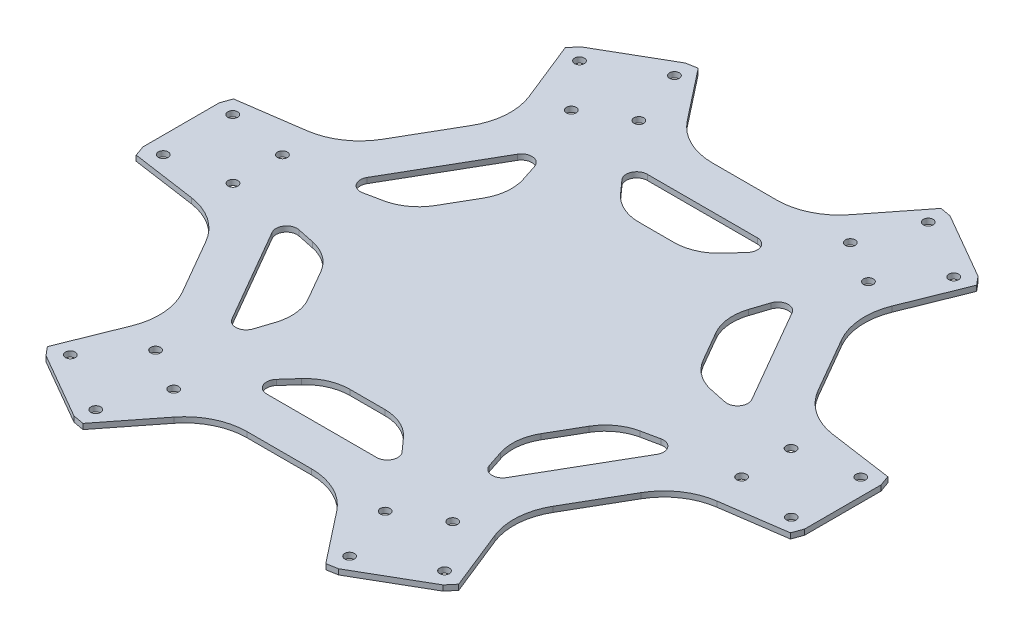
SolidWorks part; units mm, degrees
ref_plane "Front Plane" through (0, 0, 0) normal (0, 0, 1) x (1, 0, 0)
ref_plane "Top Plane" through (0, 0, 0) normal (0, 1, 0) x (1, 0, 0)
ref_plane "Right Plane" through (0, 0, 0) normal (1, 0, 0) x (0, 0, -1)
sketch "Model" plane through (0, 0, 0) normal (0, 1, 0) x (1, 0, 0)
  line L0 (-40.4555, -102.4939) -> (-44.0829, -101.8523)
  line L1 (-27.0946, -85.4828) -> (-40.4555, -102.4939)
  line L2 (-10.7284, -77.5264) -> (10.7284, -77.5264)
  line L3 (27.0946, -85.4828) -> (40.4555, -102.4939)
  line L4 (44.0829, -101.8523) -> (66.1652, -89.1031)
  line L5 (40.4555, -102.4939) -> (44.0829, -101.8523)
  line L6 (68.5346, -86.2824) -> (66.1652, -89.1031)
  line L7 (60.483, -66.206) -> (68.5346, -86.2824)
  line L8 (61.7757, -48.0543) -> (72.5041, -29.4721)
  line L9 (87.5776, -19.2768) -> (108.99, -16.2115)
  line L10 (110.2482, -12.7492) -> (110.2482, 12.7492)
  line L11 (108.99, -16.2115) -> (110.2482, -12.7492)
  line L12 (108.99, 16.2115) -> (110.2482, 12.7492)
  line L13 (87.5776, 19.2768) -> (108.99, 16.2115)
  line L14 (72.5041, 29.4721) -> (61.7757, 48.0543)
  line L15 (60.483, 66.206) -> (68.5346, 86.2824)
  line L16 (66.1652, 89.1031) -> (44.0829, 101.8523)
  line L17 (68.5346, 86.2824) -> (66.1652, 89.1031)
  line L18 (40.4555, 102.4939) -> (44.0829, 101.8523)
  line L19 (27.0946, 85.4828) -> (40.4555, 102.4939)
  line L20 (10.7284, 77.5264) -> (-10.7284, 77.5264)
  line L21 (-27.0946, 85.4828) -> (-40.4555, 102.4939)
  line L22 (-44.0829, 101.8523) -> (-66.1652, 89.1031)
  line L23 (-40.4555, 102.4939) -> (-44.0829, 101.8523)
  line L24 (-68.5346, 86.2824) -> (-66.1652, 89.1031)
  line L25 (-60.483, 66.206) -> (-68.5346, 86.2824)
  line L26 (-61.7757, 48.0543) -> (-72.5041, 29.4721)
  line L27 (-87.5776, 19.2768) -> (-108.99, 16.2115)
  line L28 (-110.2482, 12.7492) -> (-110.2482, -12.7492)
  line L29 (-108.99, 16.2115) -> (-110.2482, 12.7492)
  line L30 (-108.99, -16.2115) -> (-110.2482, -12.7492)
  line L31 (-87.5776, -19.2768) -> (-108.99, -16.2115)
  line L32 (-72.5041, -29.4721) -> (-61.7757, -48.0543)
  line L33 (-60.483, -66.206) -> (-68.5346, -86.2824)
  line L34 (-66.1652, -89.1031) -> (-44.0829, -101.8523)
  line L35 (-68.5346, -86.2824) -> (-66.1652, -89.1031)
  line L36 (18.3454, -63.4119) -> (-18.3454, -63.4119)
  line L37 (17.0052, -53.1705) -> (20.9523, -57.5765)
  line L38 (-5.8327, -48.1793) -> (5.8327, -48.1793)
  line L39 (-20.9523, -57.5765) -> (-17.0052, -53.1705)
  line L40 (64.089, -15.8183) -> (45.7436, -47.5935)
  line L41 (54.5496, -11.8583) -> (60.3389, -10.643)
  line L42 (38.8081, -29.141) -> (44.6409, -19.0383)
  line L43 (39.3866, -46.9335) -> (37.5444, -41.3122)
  line L44 (45.7436, 47.5935) -> (64.089, 15.8183)
  line L45 (37.5444, 41.3122) -> (39.3866, 46.9335)
  line L46 (44.6409, 19.0383) -> (38.8081, 29.141)
  line L47 (60.3389, 10.643) -> (54.5496, 11.8583)
  line L48 (-18.3454, 63.4119) -> (18.3454, 63.4119)
  line L49 (-17.0052, 53.1705) -> (-20.9523, 57.5765)
  line L50 (5.8327, 48.1793) -> (-5.8327, 48.1793)
  line L51 (20.9523, 57.5765) -> (17.0052, 53.1705)
  line L52 (-64.089, 15.8183) -> (-45.7436, 47.5935)
  line L53 (-54.5496, 11.8583) -> (-60.3389, 10.643)
  line L54 (-38.8081, 29.141) -> (-44.6409, 19.0383)
  line L55 (-39.3866, 46.9335) -> (-37.5444, 41.3122)
  line L56 (-45.7436, -47.5935) -> (-64.089, -15.8183)
  line L57 (-37.5444, -41.3122) -> (-39.3866, -46.9335)
  line L58 (-44.6409, -19.0383) -> (-38.8081, -29.141)
  line L59 (-60.3389, -10.643) -> (-54.5496, -11.8583)
  circle A0 centre (49.4999, -69.2617) radius 1.625
  circle A1 centre (35.2325, -77.499) radius 1.625
  circle A2 centre (42.2879, -96.4) radius 1.625
  circle A3 centre (62.3409, -84.8224) radius 1.625
  circle A4 centre (84.7323, 8.2373) radius 1.625
  circle A5 centre (84.7323, -8.2373) radius 1.625
  circle A6 centre (104.6288, -11.5776) radius 1.625
  circle A7 centre (104.6288, 11.5776) radius 1.625
  circle A8 centre (35.2325, 77.499) radius 1.625
  circle A9 centre (49.4999, 69.2617) radius 1.625
  circle A10 centre (62.3409, 84.8224) radius 1.625
  circle A11 centre (42.2879, 96.4) radius 1.625
  circle A12 centre (-49.4999, 69.2617) radius 1.625
  circle A13 centre (-35.2325, 77.499) radius 1.625
  circle A14 centre (-42.2879, 96.4) radius 1.625
  circle A15 centre (-62.3409, 84.8224) radius 1.625
  circle A16 centre (-84.7323, -8.2373) radius 1.625
  circle A17 centre (-84.7323, 8.2373) radius 1.625
  circle A18 centre (-104.6288, 11.5776) radius 1.625
  circle A19 centre (-104.6288, -11.5776) radius 1.625
  circle A20 centre (-35.2325, -77.499) radius 1.625
  circle A21 centre (-49.4999, -69.2617) radius 1.625
  circle A22 centre (-62.3409, -84.8224) radius 1.625
  circle A23 centre (-42.2879, -96.4) radius 1.625
  arc A24 (-10.7284, -77.5264) -> (-27.0946, -85.4828) centre (-10.7284, -98.3372) ccw
  arc A25 (27.0946, -85.4828) -> (10.7284, -77.5264) centre (10.7284, -98.3372) ccw
  arc A26 (61.7757, -48.0543) -> (60.483, -66.206) centre (79.7983, -58.4597) ccw
  arc A27 (87.5776, -19.2768) -> (72.5041, -29.4721) centre (90.5267, -39.8775) ccw
  arc A28 (72.5041, 29.4721) -> (87.5776, 19.2768) centre (90.5267, 39.8775) ccw
  arc A29 (60.483, 66.206) -> (61.7757, 48.0543) centre (79.7983, 58.4597) ccw
  arc A30 (10.7284, 77.5264) -> (27.0946, 85.4828) centre (10.7284, 98.3372) ccw
  arc A31 (-27.0946, 85.4828) -> (-10.7284, 77.5264) centre (-10.7284, 98.3372) ccw
  arc A32 (-61.7757, 48.0543) -> (-60.483, 66.206) centre (-79.7983, 58.4597) ccw
  arc A33 (-87.5776, 19.2768) -> (-72.5041, 29.4721) centre (-90.5267, 39.8775) ccw
  arc A34 (-72.5041, -29.4721) -> (-87.5776, -19.2768) centre (-90.5267, -39.8775) ccw
  arc A35 (-60.483, -66.206) -> (-61.7757, -48.0543) centre (-79.7983, -58.4597) ccw
  arc A36 (-20.9523, -57.5765) -> (-18.3454, -63.4119) centre (-18.3454, -59.9119) ccw
  arc A37 (18.3454, -63.4119) -> (20.9523, -57.5765) centre (18.3454, -59.9119) ccw
  arc A38 (17.0052, -53.1705) -> (5.8327, -48.1793) centre (5.8327, -63.1793) ccw
  arc A39 (-5.8327, -48.1793) -> (-17.0052, -53.1705) centre (-5.8327, -63.1793) ccw
  arc A40 (39.3866, -46.9335) -> (45.7436, -47.5935) centre (42.7125, -45.8435) ccw
  arc A41 (64.089, -15.8183) -> (60.3389, -10.643) centre (61.0579, -14.0683) ccw
  arc A42 (54.5496, -11.8583) -> (44.6409, -19.0383) centre (57.6312, -26.5383) ccw
  arc A43 (38.8081, -29.141) -> (37.5444, -41.3122) centre (51.7985, -36.641) ccw
  arc A44 (60.3389, 10.643) -> (64.089, 15.8183) centre (61.0579, 14.0683) ccw
  arc A45 (45.7436, 47.5935) -> (39.3866, 46.9335) centre (42.7125, 45.8435) ccw
  arc A46 (37.5444, 41.3122) -> (38.8081, 29.141) centre (51.7985, 36.641) ccw
  arc A47 (44.6409, 19.0383) -> (54.5496, 11.8583) centre (57.6312, 26.5383) ccw
  arc A48 (20.9523, 57.5765) -> (18.3454, 63.4119) centre (18.3454, 59.9119) ccw
  arc A49 (-18.3454, 63.4119) -> (-20.9523, 57.5765) centre (-18.3454, 59.9119) ccw
  arc A50 (-17.0052, 53.1705) -> (-5.8327, 48.1793) centre (-5.8327, 63.1793) ccw
  arc A51 (5.8327, 48.1793) -> (17.0052, 53.1705) centre (5.8327, 63.1793) ccw
  arc A52 (-39.3866, 46.9335) -> (-45.7436, 47.5935) centre (-42.7125, 45.8435) ccw
  arc A53 (-64.089, 15.8183) -> (-60.3389, 10.643) centre (-61.0579, 14.0683) ccw
  arc A54 (-54.5496, 11.8583) -> (-44.6409, 19.0383) centre (-57.6312, 26.5383) ccw
  arc A55 (-38.8081, 29.141) -> (-37.5444, 41.3122) centre (-51.7985, 36.641) ccw
  arc A56 (-60.3389, -10.643) -> (-64.089, -15.8183) centre (-61.0579, -14.0683) ccw
  arc A57 (-45.7436, -47.5935) -> (-39.3866, -46.9335) centre (-42.7125, -45.8435) ccw
  arc A58 (-37.5444, -41.3122) -> (-38.8081, -29.141) centre (-51.7985, -36.641) ccw
  arc A59 (-44.6409, -19.0383) -> (-54.5496, -11.8583) centre (-57.6312, -26.5383) ccw
extrude "Boss-Extrude1" add sketch "Model" along normal blind 1.8
